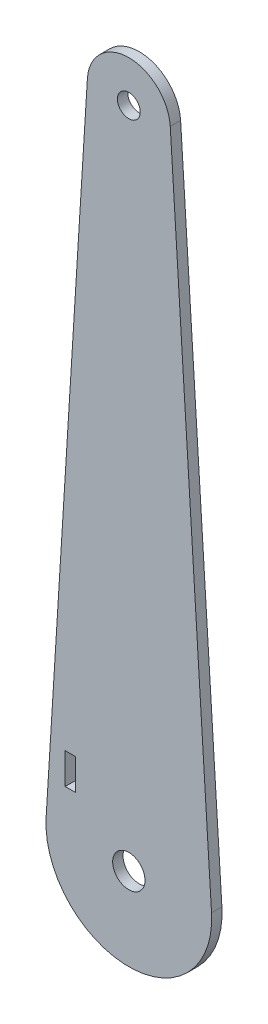
SolidWorks part; units mm, degrees
ref_plane "Front Plane" through (0, 0, 0) normal (0, 0, 1) x (1, 0, 0)
ref_plane "Top Plane" through (0, 0, 0) normal (0, 1, 0) x (1, 0, 0)
ref_plane "Right Plane" through (0, 0, 0) normal (1, 0, 0) x (0, 0, -1)
sketch "Sketch1" plane through (0, 0, 0) normal (0, 0, 1) x (1, 0, 0)
  line L0 (-25.3505, 1.5844) -> (-12.7, 203.9937)
  line L1 (25.3505, 1.5844) -> (12.7, 203.9937)
  line L19 (-19.5072, 22.225) -> (-16.3322, 22.225)
  line L20 (-19.5072, 22.225) -> (-19.5072, 12.7)
  line L21 (-19.5072, 12.7) -> (-16.3322, 12.7)
  line L22 (-16.3322, 22.225) -> (-16.3322, 12.7)
  circle A0 centre (0, 0) radius 4.953
  arc A1 (25.3505, 1.5844) -> (-25.3505, 1.5844) centre (0, 0) cw
  arc A2 (-12.7, 203.9937) -> (12.7, 203.9937) centre (0, 203.2) cw
  circle A3 centre (0, 203.2) radius 3.5
  dimension "D1" = 9.906
  dimension "D2" = 25.4
  dimension "D5" = 7
  dimension "D3" = 25.4
  dimension "D4" = 203.2
  dimension "D6" = 3.175
  dimension "D7" = 16.3322
  dimension "D8" = 9.525
  dimension "D9" = 12.7
extrude "Boss-Extrude1" add sketch "Sketch1" along normal blind 3.175
